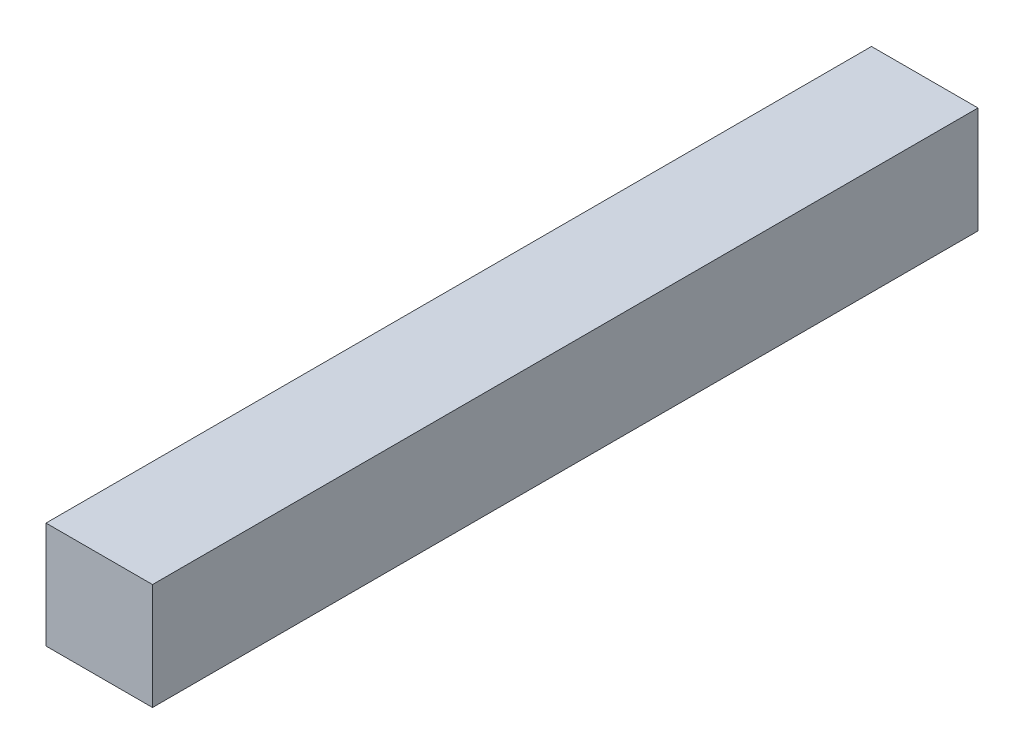
SolidWorks part; units mm, degrees
ref_plane "Front Plane" through (0, 0, 0) normal (0, 0, 1) x (1, 0, 0)
ref_plane "Top Plane" through (0, 0, 0) normal (0, 1, 0) x (1, 0, 0)
ref_plane "Right Plane" through (0, 0, 0) normal (1, 0, 0) x (0, 0, -1)
sketch "Sketch1" plane through (0, 0, 0) normal (0, 0, 1) x (1, 0, 0)
  line L1 (0, 0) -> (25.4, 0)
  line L2 (0, 0) -> (0, 25.4)
  line L3 (0, 25.4) -> (25.4, 25.4)
  line L4 (25.4, 0) -> (25.4, 25.4)
  dimension "D1" = 25.4
  dimension "D2" = 25.4
extrude "Boss-Extrude1" add sketch "Sketch1" along normal blind 196.85
